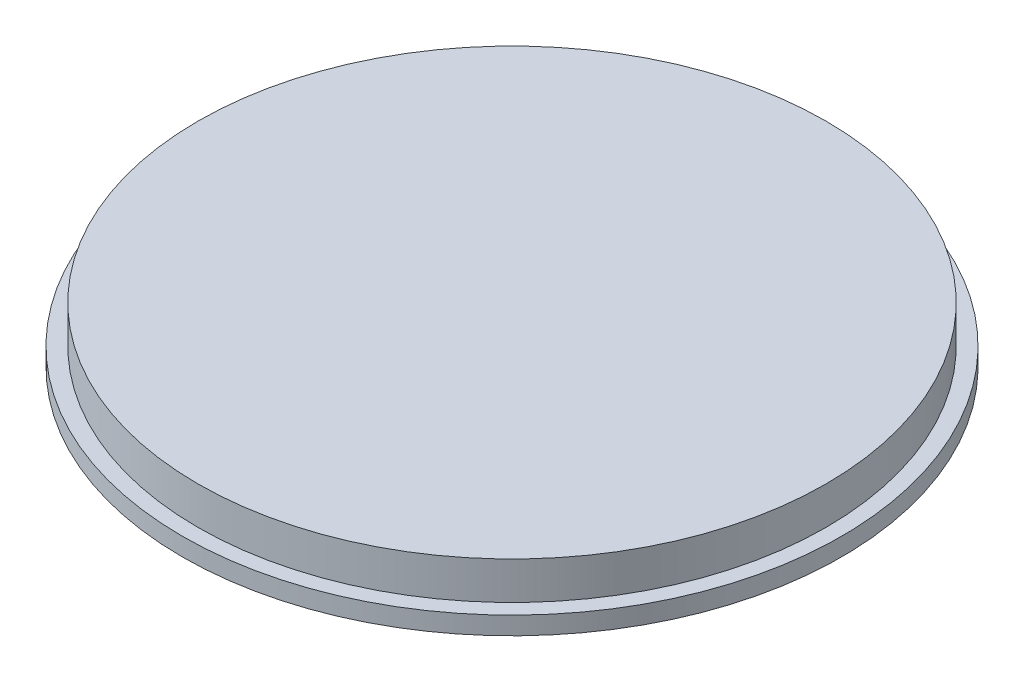
SolidWorks part; units mm, degrees
ref_plane "Front Plane" through (0, 0, 0) normal (0, 0, 1) x (1, 0, 0)
ref_plane "Top Plane" through (0, 0, 0) normal (0, 1, 0) x (1, 0, 0)
ref_plane "Right Plane" through (0, 0, 0) normal (1, 0, 0) x (0, 0, -1)
sketch "Sketch1" plane through (0, 0, 0) normal (0, 1, 0) x (1, 0, 0)
  circle A0 centre (0, 0) radius 466.344
  dimension "D1" = 932.688
extrude "Extrude1" add sketch "Sketch1" along normal blind 25.4
sketch "Sketch2" plane through (0, 25.4, 0) normal (0, 1, 0) x (1, 0, 0)
  circle A0 centre (0, 0) radius 444.5
  dimension "D1" = 889
extrude "Extrude2" add sketch "Sketch2" along normal blind 53.34
